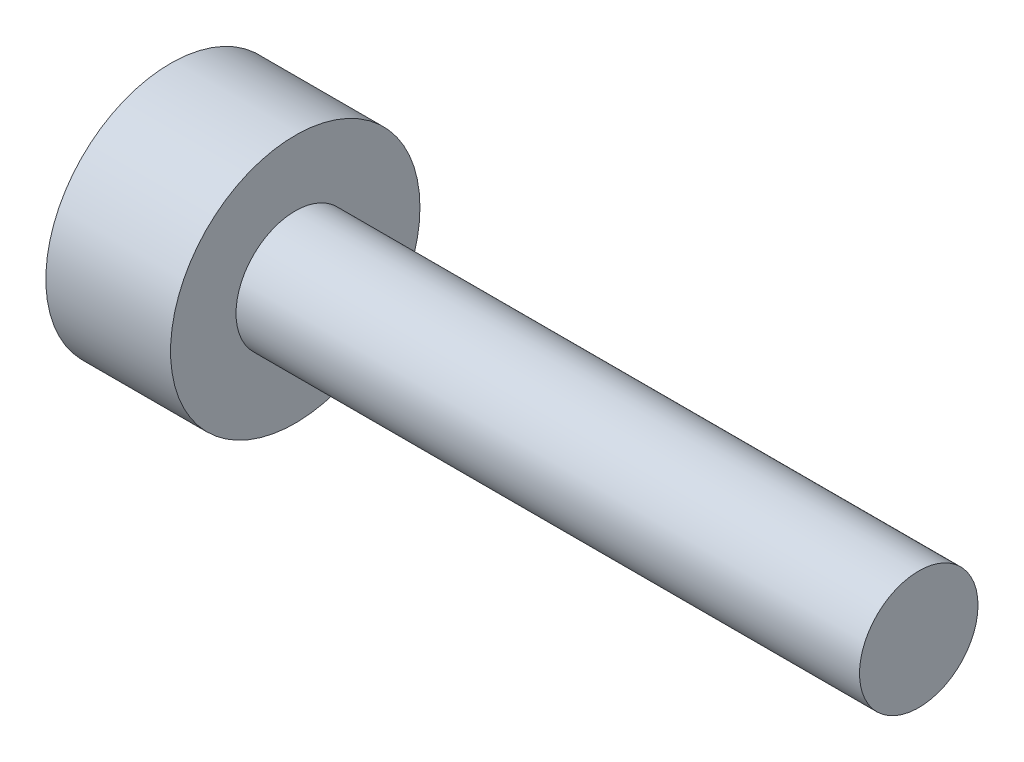
SolidWorks part; units mm, degrees
ref_plane "Front Plane" through (0, 0, 0) normal (0, 0, 1) x (1, 0, 0)
ref_plane "Top Plane" through (0, 0, 0) normal (0, 1, 0) x (1, 0, 0)
ref_plane "Right Plane" through (0, 0, 0) normal (1, 0, 0) x (0, 0, -1)
sketch "Sketch1" plane through (0, 0, 0) normal (1, 0, 0) x (0, 0, -1)
  circle A0 centre (0, 0) radius 10
  dimension "D1" = 20
extrude "Boss-Extrude1" add sketch "Sketch1" along normal blind 10
sketch "Sketch2" plane through (10, 0, 0) normal (1, 0, 0) x (0, 0, -1)
  circle A0 centre (0, 0) radius 4.75
  dimension "D1" = 9.5
extrude "Boss-Extrude2" add sketch "Sketch2" along normal blind 50
